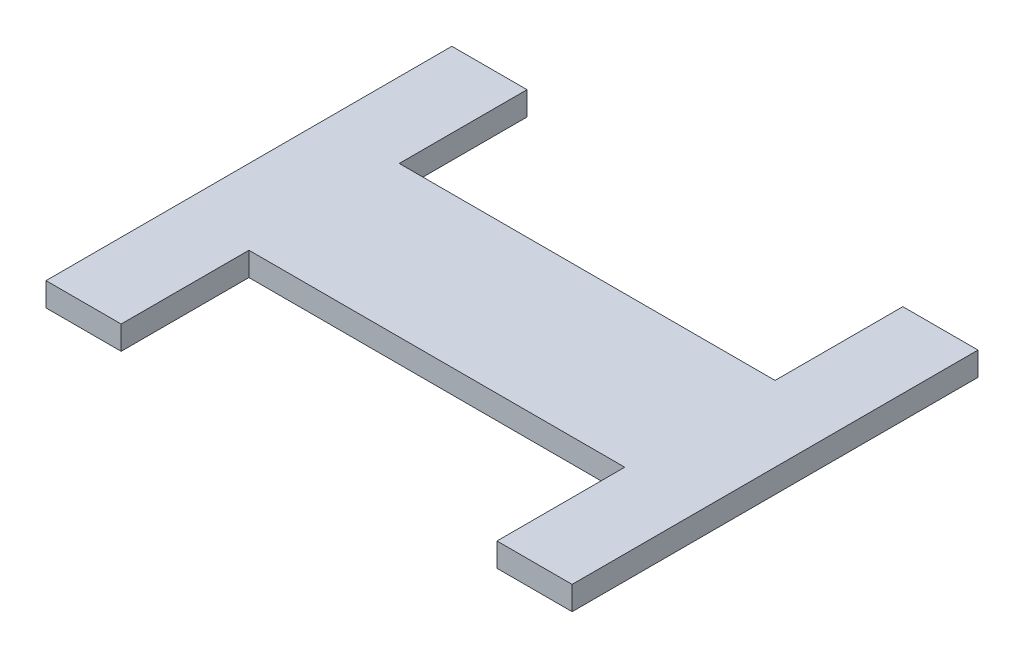
SolidWorks part; units mm, degrees
ref_plane "Front Plane" through (0, 0, 0) normal (0, 0, 1) x (1, 0, 0)
ref_plane "Top Plane" through (0, 0, 0) normal (0, 1, 0) x (1, 0, 0)
ref_plane "Right Plane" through (0, 0, 0) normal (1, 0, 0) x (0, 0, -1)
sketch "Sketch1" plane through (0, 0, 0) normal (0, 1, 0) x (1, 0, 0)
  line L1 (38.1, -38.1) -> (-38.1, -38.1) construction
  line L2 (38.1, -38.1) -> (38.1, 38.1) construction
  line L3 (38.1, 38.1) -> (-38.1, 38.1) construction
  line L4 (-38.1, -38.1) -> (-38.1, 38.1) construction
  line L5 (38.1, -38.1) -> (-38.1, 38.1) construction
  line L6 (38.1, 38.1) -> (-38.1, -38.1) construction
  line L7 (44.45, -12.7) -> (-44.45, -12.7)
  line L8 (44.45, -12.7) -> (44.45, 12.7)
  line L9 (44.45, 12.7) -> (-44.45, 12.7)
  line L10 (-44.45, -12.7) -> (-44.45, 12.7)
  line L11 (44.45, -12.7) -> (-44.45, 12.7) construction
  line L12 (44.45, 12.7) -> (-44.45, -12.7) construction
  line L13 (-44.45, 12.7) -> (-31.75, 12.7)
  line L14 (-44.45, 12.7) -> (-44.45, 34.29)
  line L15 (-44.45, 34.29) -> (-31.75, 34.29)
  line L16 (-31.75, 12.7) -> (-31.75, 34.29)
  circle A0 centre (-38.1, 38.1) radius 3.81
  circle A1 centre (38.1, 38.1) radius 3.81
  circle A2 centre (-38.1, -38.1) radius 3.81
  circle A3 centre (38.1, -38.1) radius 3.81
  point P0 (0, 0)
  point P10 (0, 0)
  dimension "D3" = 7.62
  dimension "D1" = 76.2
  dimension "D2" = 76.2
  dimension "D4" = 25.4
  dimension "D5" = 44.45
  dimension "D6" = 12.7
extrude "Boss-Extrude1" add sketch "Sketch1" along normal blind 4 contours L10 L7 L8 L9 | L9 L16 L15 L14
ref_plane "Plane1" through (0, 0, 0) normal (0, 0, 1) x (1, 0, 0)
ref_plane "Plane2" through (0, 0, 0) normal (-1, 0, 0) x (0, 0, 1)
mirror "Mirror1" about plane through (0, 0, 0) normal (-1, 0, 0) of "Boss-Extrude1"
mirror "Mirror2" about plane through (0, 0, 0) normal (0, 0, 1) of "Boss-Extrude1"
mirror "Mirror3" about plane through (0, 0, 0) normal (-1, 0, 0) of "Boss-Extrude1", "Mirror2"
